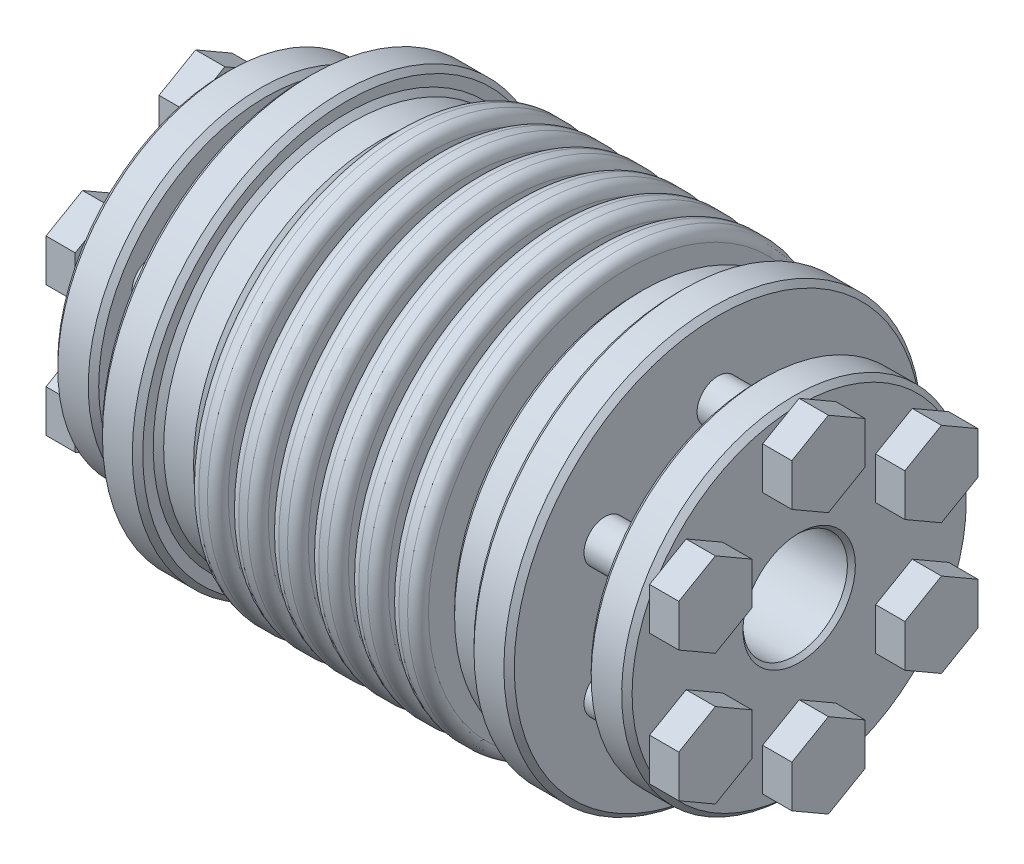
SolidWorks part; units mm, degrees
ref_plane "Front Plane" through (0, 0, 0) normal (0, 0, 1) x (1, 0, 0)
ref_plane "Top Plane" through (0, 0, 0) normal (0, 1, 0) x (1, 0, 0)
ref_plane "Right Plane" through (0, 0, 0) normal (1, 0, 0) x (0, 0, -1)
sketch "Sketch1" plane through (0, 0, 0) normal (1, 0, 0) x (0, 0, -1)
  circle A0 centre (0, 0) radius 20
  dimension "dim D" = 40
extrude "Boss-Extrude1" add sketch "Sketch1" along normal mid plane 55
sketch "Sketch2" plane through (27.5, 0, 0) normal (1, 0, 0) x (0, 0, -1)
  circle A0 centre (0, 0) radius 5
  dimension "dim d1" = 10
extrude "Cut-Extrude1" cut sketch "Sketch2" against normal blind 19
mirror "Mirror3" about plane through (0, 0, 0) normal (1, 0, 0) of "Cut-Extrude1"
chamfer "Chamfer1" distance 0.381 angle 45 4 edges at (-27.5, 0, -20) (27.5, 0, -20) (27.5, 0, -5) (-27.5, 0, -5)
ref_plane "L1" through (8.5, 0, 0) normal (1, 0, 0) x (0, 0, -1)
sketch "Sketch5" plane through (0, 0, 0) normal (1, 0, 0) x (0, 0, -1)
  line L0 (0, 5.381) -> (0, 20) construction
  circle A0 centre (0, 0) radius 5.381 construction
  circle A1 centre (0, 0) radius 12.6905
  circle A3 centre (0, 0) radius 20 construction
  point P9 (0, 12.6905)
extrude "Cut-Extrude2" cut sketch "Sketch5" against normal up to surface and the other way up to surface up to face at (-8.5, 0, -5) other way up to face at (8.5, 0, -5)
sketch "Sketch8" plane through (0, 0, 0) normal (0, 1, 0) x (1, 0, 0)
  line L0 (8.5, 12.6905) -> (-8.5, 12.6905) construction
  line L2 (-0.5, 14.6905) -> (0.5, 14.6905)
  line L3 (-0.5, 14.6905) -> (-0.5, 20)
  line L4 (-0.5, 20) -> (0.5, 20)
  line L5 (0, 14.6905) -> (0, 0) construction
  line L6 (0.5, 14.6905) -> (0.5, 20)
  line L7 (0, 0) -> (27.5, 0) construction
  line L8 (27.5, -19.619) -> (27.5, 19.619) construction
  line L9 (8.5, 5) -> (8.5, -5) construction
  line L10 (8.5, 5) -> (8.5, -5) construction
  line L11 (-27.5, -14.6905) -> (27.5, -14.6905) construction
  line L13 (0.5, 14.6905) -> (1.27, 14.6905) construction
  line L14 (-27.5, 19.619) -> (-27.5, -19.619) construction
  line L15 (3.3333, 14.6905) -> (4.3333, 14.6905)
  line L16 (3.3333, 14.6905) -> (3.3333, 20)
  line L17 (3.3333, 20) -> (4.3333, 20)
  line L18 (4.3333, 14.6905) -> (4.3333, 20)
  line L19 (7.1667, 14.6905) -> (8.1667, 14.6905)
  line L20 (7.1667, 14.6905) -> (7.1667, 20)
  line L21 (7.1667, 20) -> (8.1667, 20)
  line L22 (8.1667, 14.6905) -> (8.1667, 20)
  line L23 (11, 14.6905) -> (12, 14.6905)
  line L24 (11, 14.6905) -> (11, 20)
  line L25 (11, 20) -> (12, 20)
  line L26 (12, 14.6905) -> (12, 20)
  line L27 (-0.5, 14.6905) -> (3.3333, 14.6905) construction
  line L28 (0, 0) -> (0, -14.6905) construction
  dimension "D2" = 4
  dimension "D1" = 1
  dimension "D3" = 2
  dimension "Dim L2" = 24
revolve "Cut-Revolve1" cut sketch "Sketch8" angle 360 about L7
mirror "Mirror2" about plane through (0, 0, 0) normal (1, 0, 0) of "Cut-Revolve1"
fillet "Fillet1" radius 1 14 edges at (0.5, 0, 20) (-0.5, 0, 20) (12, 0, 20) (11, 0, 20) (8.1667, 0, 20) (7.1667, 0, 20) (4.3333, 0, 20) (3.3333, 0, 20) (-11, 0, 20) (-8.1667, 0, 20) (-7.1667, 0, 20) (-4.3333, 0, 20) (-3.3333, 0, 20) (-12, 0, 20)
fillet "Fillet2" radius 0.25 14 edges at (-7.1667, 0, 14.6905) (-3.3333, 0, 14.6905) (0.5, 0, 14.6905) (4.3333, 0, 14.6905) (8.1667, 0, 14.6905) (12, 0, 14.6905) (11, 0, 14.6905) (7.1667, 0, 14.6905) (3.3333, 0, 14.6905) (-0.5, 0, 14.6905) (-4.3333, 0, 14.6905) (-8.1667, 0, 14.6905) (-11, 0, 14.6905) (-12, 0, 14.6905)
sketch "Sketch9" plane through (0, 0, 0) normal (0, 0, 1) x (1, 0, 0)
  line L0 (12, 18) -> (15.8601, 18)
  line L1 (12, 19) -> (12, -19) construction
  line L2 (15.8601, 18) -> (15.8601, 20)
  line L3 (27.119, 20) -> (13, 20) construction
  line L4 (15.8601, 20) -> (19.7202, 20)
  line L5 (19.7202, 20) -> (19.7202, 7.8194)
  line L6 (19.7202, 7.8194) -> (23.5803, 8.5)
  line L7 (23.5803, 8.5) -> (23.5803, 16.5)
  line L8 (23.5803, 16.5) -> (27.5, 16.5)
  line L9 (27.5, -19.619) -> (27.5, 19.619) construction
  line L10 (27.5, 16.5) -> (27.5, 25)
  line L11 (27.5, 25) -> (12, 25)
  line L12 (12, 25) -> (12, 18)
  line L13 (23.5803, 8.5) -> (19.7202, 8.5) construction
  line L14 (27.119, 5) -> (27.119, 20) construction
  line L15 (27.119, 12.5) -> (23.5803, 12.5) construction
  line L16 (27.5, 0) -> (-27.5, 0) construction
  line L17 (-27.5, 19.619) -> (-27.5, -19.619) construction
  line L18 (0, 0) -> (0, -27.1776) construction
  line L19 (-27.119, 12.5) -> (-23.5803, 12.5) construction
  line L20 (-27.119, 5) -> (-27.119, 20) construction
  line L21 (-23.5803, 8.5) -> (-19.7202, 8.5) construction
  line L22 (-12, 25) -> (-12, 18)
  line L23 (-27.5, 25) -> (-12, 25)
  line L24 (-27.5, 16.5) -> (-27.5, 25)
  line L25 (-23.5803, 16.5) -> (-27.5, 16.5)
  line L26 (-23.5803, 8.5) -> (-23.5803, 16.5)
  line L27 (-19.7202, 7.8194) -> (-23.5803, 8.5)
  line L28 (-19.7202, 20) -> (-19.7202, 7.8194)
  line L29 (-15.8601, 20) -> (-19.7202, 20)
  line L30 (-15.8601, 18) -> (-15.8601, 20)
  line L31 (-12, 18) -> (-15.8601, 18)
  dimension "D1" = 5
  dimension "D2" = 2
  dimension "D3" = 4
  dimension "D4" = 4
  dimension "D5" = 10
revolve "Cut-Revolve2" cut sketch "Sketch9" angle 360 about L16
sketch "Sketch10" plane through (27.5, 0, 0) normal (1, 0, 0) x (0, 0, -1)
  line L0 (0, 8.5) -> (0, 16.5) construction
  line L1 (7.3253, 4.2293) -> (10.8253, 2.2085)
  line L2 (0, 8.4585) -> (3.5, 10.4793)
  line L3 (3.5, 10.4793) -> (3.5, 14.5207)
  line L4 (3.5, 14.5207) -> (0, 16.5415)
  line L5 (0, 16.5415) -> (-3.5, 14.5207)
  line L6 (-3.5, 14.5207) -> (-3.5, 10.4793)
  line L7 (-3.5, 10.4793) -> (0, 8.4585)
  line L8 (10.8253, 2.2085) -> (14.3253, 4.2293)
  line L9 (14.3253, 4.2293) -> (14.3253, 8.2707)
  line L10 (14.3253, 8.2707) -> (10.8253, 10.2915)
  line L11 (10.8253, 10.2915) -> (7.3253, 8.2707)
  line L12 (7.3253, 8.2707) -> (7.3253, 4.2293)
  line L13 (7.3612, 4.25) -> (14.2894, 8.25) construction
  line L14 (7.3253, -4.2293) -> (7.3253, -8.2707)
  line L15 (7.3253, -8.2707) -> (10.8253, -10.2915)
  line L16 (10.8253, -10.2915) -> (14.3253, -8.2707)
  line L17 (14.3253, -8.2707) -> (14.3253, -4.2293)
  line L18 (14.3253, -4.2293) -> (10.8253, -2.2085)
  line L19 (10.8253, -2.2085) -> (7.3253, -4.2293)
  line L20 (7.3612, -4.25) -> (14.2894, -8.25) construction
  line L21 (0, -8.4585) -> (-3.5, -10.4793)
  line L22 (-3.5, -10.4793) -> (-3.5, -14.5207)
  line L23 (-3.5, -14.5207) -> (0, -16.5415)
  line L24 (0, -16.5415) -> (3.5, -14.5207)
  line L25 (3.5, -14.5207) -> (3.5, -10.4793)
  line L26 (3.5, -10.4793) -> (0, -8.4585)
  line L27 (0, -8.5) -> (0, -16.5) construction
  line L28 (-7.3253, -4.2293) -> (-10.8253, -2.2085)
  line L29 (-10.8253, -2.2085) -> (-14.3253, -4.2293)
  line L30 (-14.3253, -4.2293) -> (-14.3253, -8.2707)
  line L31 (-14.3253, -8.2707) -> (-10.8253, -10.2915)
  line L32 (-10.8253, -10.2915) -> (-7.3253, -8.2707)
  line L33 (-7.3253, -8.2707) -> (-7.3253, -4.2293)
  line L34 (-7.3612, -4.25) -> (-14.2894, -8.25) construction
  line L35 (-7.3253, 4.2293) -> (-7.3253, 8.2707)
  line L36 (-7.3253, 8.2707) -> (-10.8253, 10.2915)
  line L37 (-10.8253, 10.2915) -> (-14.3253, 8.2707)
  line L38 (-14.3253, 8.2707) -> (-14.3253, 4.2293)
  line L39 (-14.3253, 4.2293) -> (-10.8253, 2.2085)
  line L40 (-10.8253, 2.2085) -> (-7.3253, 4.2293)
  line L41 (-7.3612, 4.25) -> (-14.2894, 8.25) construction
  circle A0 centre (0, 0) radius 12.5 construction
  circle A1 centre (0, 0) radius 8.5 construction
  circle A2 centre (0, 0) radius 8.5 construction
  circle A3 centre (0, 0) radius 16.5 construction
  circle A4 centre (0, 12.5) radius 3.5 construction
  circle A5 centre (10.8253, 6.25) radius 3.5 construction
  circle A6 centre (10.8253, -6.25) radius 3.5 construction
  circle A7 centre (0, -12.5) radius 3.5 construction
  circle A8 centre (-10.8253, -6.25) radius 3.5 construction
  circle A9 centre (-10.8253, 6.25) radius 3.5 construction
  point P10 (0, 12.5)
  point P24 (10.8253, 6.25)
  point P35 (10.8253, -6.25)
  point P46 (0, -12.5)
  point P57 (-10.8253, -6.25)
  point P68 (-10.8253, 6.25)
  dimension "D1" = 6
  dimension "Dim Hex Head Width" = 7
extrude "Boss-Extrude2" add sketch "Sketch10" along normal blind 2.8 separate body
sketch "Sketch11" plane through (30.3, 0, 0) normal (1, 0, 0) x (0, 0, -1)
  line L0 (0, 16.5415) -> (0, 8.4585) construction
  line L1 (7.3253, 4.2293) -> (14.3253, 8.2707) construction
  circle A0 centre (0, 12.5) radius 2
  circle A1 centre (10.8253, 6.25) radius 2
  circle A2 centre (10.8253, -6.25) radius 2
  circle A3 centre (0, -12.5) radius 2
  circle A4 centre (-10.8253, -6.25) radius 2
  circle A5 centre (-10.8253, 6.25) radius 2
  dimension "D1" = 6
  dimension "Dim M" = 4
extrude "Boss-Extrude3" add sketch "Sketch11" against normal up to surface (10.5798 mm away) up to face at (19.7202, 7.8194, 0)
mirror "Mirror5" about plane through (0, 0, 0) normal (1, 0, 0) of bodies 123 124 125 126 127 128
chamfer "Chamfer2" distance 0.5 angle 45 12 edges at (23.5803, 16.5, 0) (27.5, 16.5, 0) (19.7202, 20, 0) (15.8601, 20, 0) (12, 18, 0) (15.8601, 18, 0) (-27.5, 16.5, 0) (-23.5803, 16.5, 0) (-19.7202, 20, 0) (-15.8601, 20, 0) (-15.8601, 18, 0) (-12, 18, 0)
